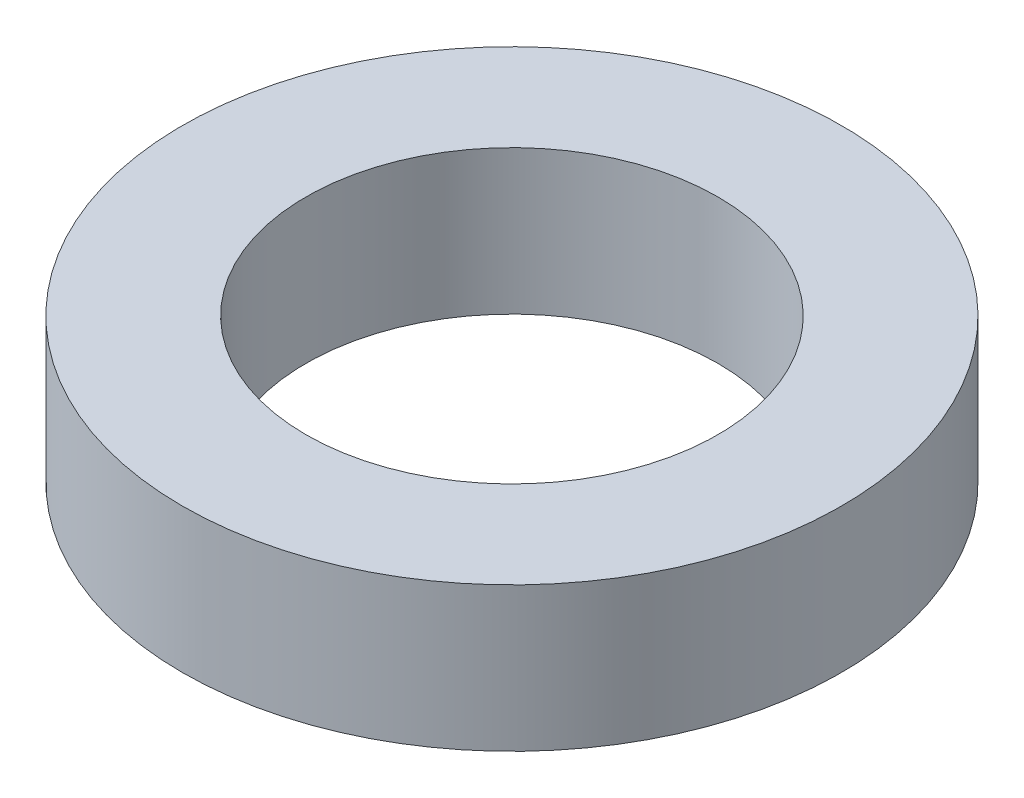
SolidWorks part; units mm, degrees
material "1060 Alloy"
ref_plane "Front Plane" through (0, 0, 0) normal (0, 0, 1) x (1, 0, 0)
ref_plane "Top Plane" through (0, 0, 0) normal (0, 1, 0) x (1, 0, 0)
ref_plane "Right Plane" through (0, 0, 0) normal (1, 0, 0) x (0, 0, -1)
sketch "Sketch1" plane through (0, 0, 0) normal (0, 1, 0) x (1, 0, 0)
  circle A0 centre (0, 0) radius 16
  circle A1 centre (0, 0) radius 10
  dimension "D1" = 32
  dimension "D2" = 20
extrude "Boss-Extrude1" add sketch "Sketch1" along normal blind 7
